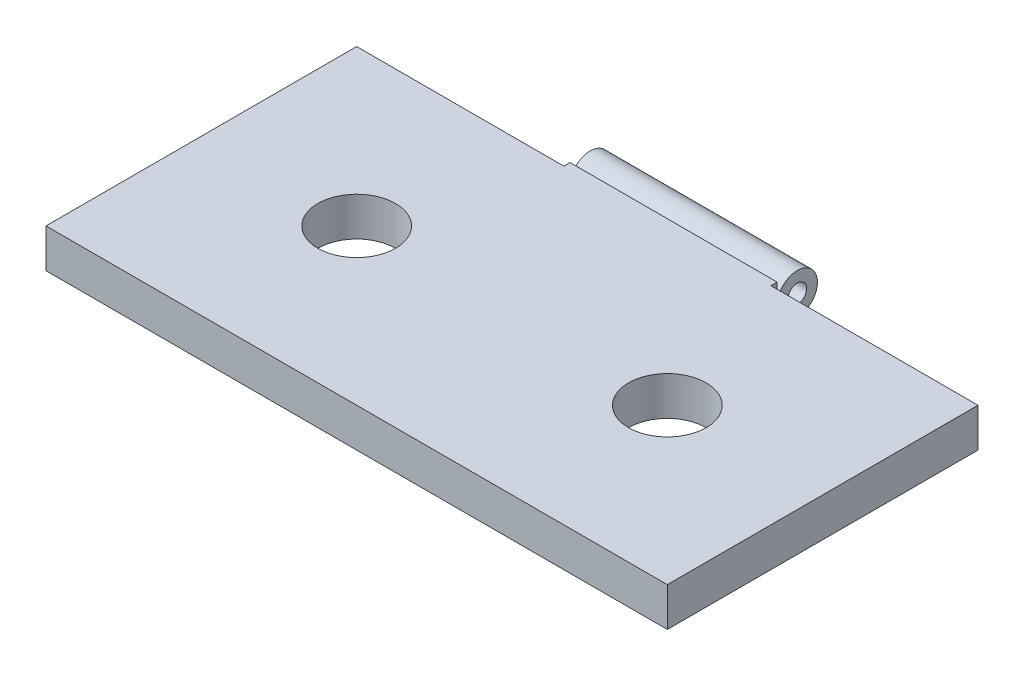
SolidWorks part; units mm, degrees
ref_plane "Alzado" through (0, 0, 0) normal (0, 0, 1) x (1, 0, 0)
ref_plane "Planta" through (0, 0, 0) normal (0, 1, 0) x (1, 0, 0)
ref_plane "Vista lateral" through (0, 0, 0) normal (1, 0, 0) x (0, 0, -1)
sketch "Croquis3" plane through (0, 0, 0) normal (0, 1, 0) x (1, 0, 0)
  line L1 (25.4, -12.7) -> (-25.4, -12.7)
  line L2 (25.4, -12.7) -> (25.4, 12.7)
  line L3 (25.4, 12.7) -> (-25.4, 12.7)
  line L4 (-25.4, -12.7) -> (-25.4, 12.7)
  line L5 (25.4, -12.7) -> (-25.4, 12.7) construction
  line L6 (25.4, 12.7) -> (-25.4, -12.7) construction
  circle A0 centre (-12.7, 0) radius 3.175
  circle A1 centre (12.7, 0) radius 3.175
  point P0 (0, 0)
  dimension "D5" = 6.35
  dimension "D6" = 6.35
  dimension "D1" = 25.4
  dimension "D2" = 50.8
  dimension "D3" = 12.7
  dimension "D4" = 12.7
extrude "Saliente-Extruir1" add sketch "Croquis3" along normal blind 3.175
ref_plane "Plano1" through (0, 0, 0) normal (-1, 0, 0) x (0, 0, 1)
sketch "Croquis4" plane through (-25.4, 0, 0) normal (-1, 0, 0) x (0, 0, 1)
  line L0 (13.97, 0) -> (-13.97, 0) construction
  line L1 (12.7, 3.175) -> (13.208, 3.175)
  line L2 (12.7, 3.175) -> (12.7, 0)
  line L3 (12.7, 0) -> (13.208, 0)
  line L4 (13.208, 3.175) -> (13.208, 2.2784)
  line L5 (13.208, 0.9103) -> (13.208, 0)
  circle A0 centre (14.9761, 1.5944) radius 0.762
  arc A1 (13.208, 2.2784) -> (13.4522, 2.2296) centre (13.335, 2.2784) ccw
  arc A2 (13.4522, 0.9592) -> (13.208, 0.9103) centre (13.335, 0.9103) ccw
  arc A3 (13.4522, 0.9592) -> (13.4522, 2.2296) centre (14.9761, 1.5944) ccw
  dimension "D2" = 0.254
  dimension "D3" = 0.254
  dimension "D4" = 3.302
  dimension "D5" = 1.524
  dimension "D1" = 0.508
extrude "Saliente-Extruir2" [suppressed] add sketch "Croquis4" along normal mid plane 16.9333
sketch "Croquis6" plane through (0, 0, 0) normal (-1, 0, 0) x (0, 0, 1)
  line L0 (16.0596, 0) -> (-16.0596, 0) construction
  line L1 (-12.7, 3.175) -> (-13.208, 3.175)
  line L2 (-12.7, 3.175) -> (-12.7, 0)
  line L3 (-12.7, 0) -> (-13.208, 0)
  line L4 (-13.208, 3.175) -> (-13.208, 2.4375)
  line L5 (-13.208, 0.6059) -> (-13.208, 0)
  arc A0 (-13.208, 0.6059) -> (-13.4439, 0.6713) centre (-13.335, 0.6059) ccw
  arc A1 (-13.4439, 2.3721) -> (-13.4439, 0.6713) centre (-14.859, 1.5217) ccw
  arc A2 (-13.4439, 2.3721) -> (-13.208, 2.4375) centre (-13.335, 2.4375) ccw
  circle A3 centre (-14.859, 1.5217) radius 0.762
  dimension "D2" = 0.254
  dimension "D3" = 0.254
  dimension "D4" = 3.302
  dimension "D5" = 1.524
  dimension "D1" = 0.508
extrude "Saliente-Extruir3" add sketch "Croquis6" along normal mid plane 16.9333
